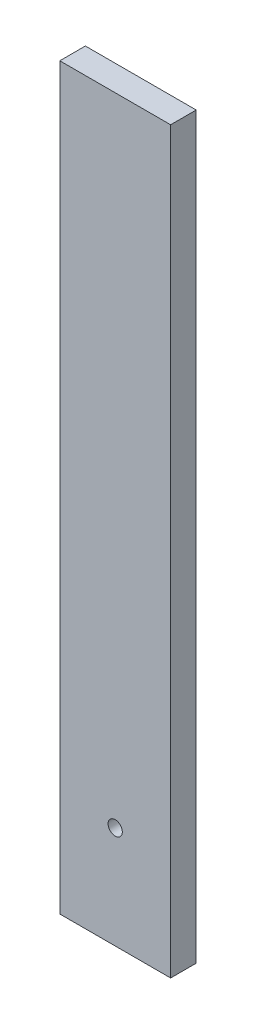
SolidWorks part; units mm, degrees
ref_plane "Front Plane" through (0, 0, 0) normal (0, 0, 1) x (1, 0, 0)
ref_plane "Top Plane" through (0, 0, 0) normal (0, 1, 0) x (1, 0, 0)
ref_plane "Right Plane" through (0, 0, 0) normal (1, 0, 0) x (0, 0, -1)
sketch "Sketch1" plane through (0, 0, 0) normal (0, 1, 0) x (1, 0, 0)
  line L1 (-97.5, 22.5) -> (97.5, 22.5)
  line L2 (-97.5, 22.5) -> (-97.5, -22.5)
  line L3 (-97.5, -22.5) -> (97.5, -22.5)
  line L4 (97.5, 22.5) -> (97.5, -22.5)
  line L5 (-97.5, 22.5) -> (97.5, -22.5) construction
  line L6 (-97.5, -22.5) -> (97.5, 22.5) construction
  point P0 (0, 0)
  dimension "D1" = 45
  dimension "D2" = 195
extrude "Shape" add sketch "Sketch1" along normal blind 1300
sketch "Sketch2" plane through (0, 0, 22.5) normal (0, 0, 1) x (1, 0, 0)
  line L0 (0, 0) -> (0, 1300) construction
  line L1 (-97.5, 1300) -> (97.5, 1300) construction
  circle A0 centre (0, 180) radius 12.5
  dimension "D1" = 25
  dimension "D2" = 180
extrude "Cut-Extrude1" cut sketch "Sketch2" against normal up to next
sketch "Sketch3" [suppressed] plane through (0, 0, 22.5) normal (0, 0, 1) x (1, 0, 0)
  circle A0 centre (0, 1150) radius 12.5 construction
  circle A1 centre (0, 1150) radius 12.5
extrude "Cut-Extrude2" [suppressed] cut sketch "Sketch3" against normal up to next
